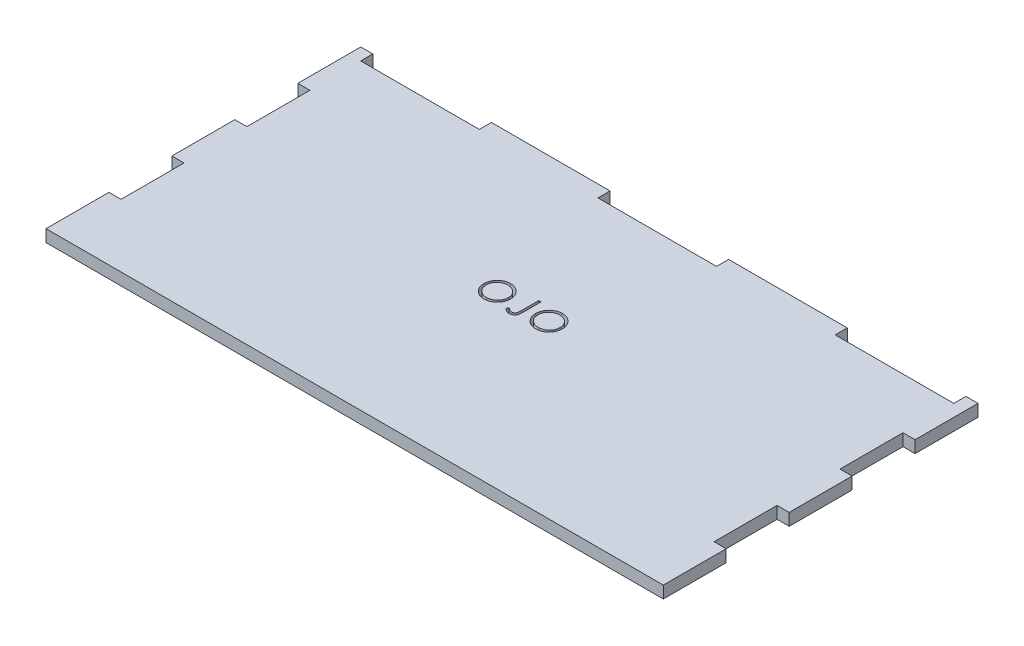
SolidWorks part; units mm, degrees
ref_plane "Front Plane" through (0, 0, 0) normal (0, 0, 1) x (1, 0, 0)
ref_plane "Top Plane" through (0, 0, 0) normal (0, 1, 0) x (1, 0, 0)
ref_plane "Right Plane" through (0, 0, 0) normal (1, 0, 0) x (0, 0, -1)
sketch "Sketch1" plane through (0, 0, 0) normal (0, 1, 0) x (1, 0, 0)
  line L6 (-73.5, 33) -> (-44.1, 33)
  line L12 (-73.5, 20.4) -> (-73.5, 4.8)
  line L14 (-76.5, 36) -> (-73.5, 36)
  line L16 (-76.5, 36) -> (-76.5, 20.4)
  line L20 (-76.5, 4.8) -> (-76.5, -10.8)
  line L23 (-76.5, -26.4) -> (-76.5, -42)
  line L24 (-76.5, -26.4) -> (-73.5, -26.4)
  line L25 (-76.5, -10.8) -> (-73.5, -10.8)
  line L26 (-76.5, 4.8) -> (-73.5, 4.8)
  line L27 (-76.5, 20.4) -> (-73.5, 20.4)
  line L29 (-73.5, 33) -> (-73.5, 36)
  line L30 (-73.5, -10.8) -> (-73.5, -26.4)
  line L31 (14.7, 36) -> (44.1, 36)
  line L32 (76.5, -26.4) -> (76.5, -42)
  line L33 (76.5, -26.4) -> (73.5, -26.4)
  line L34 (73.5, -10.8) -> (73.5, -26.4)
  line L35 (76.5, -10.8) -> (73.5, -10.8)
  line L36 (76.5, 4.8) -> (76.5, -10.8)
  line L37 (76.5, 4.8) -> (73.5, 4.8)
  line L38 (73.5, 20.4) -> (73.5, 4.8)
  line L39 (76.5, 20.4) -> (73.5, 20.4)
  line L40 (76.5, 36) -> (76.5, 20.4)
  line L41 (73.5, 33) -> (73.5, 36)
  line L43 (-14.7, 33) -> (14.7, 33)
  line L44 (73.5, 36) -> (76.5, 36)
  line L45 (44.1, 33) -> (73.5, 33)
  line L46 (-44.1, 33) -> (-44.1, 36)
  line L47 (-14.7, 33) -> (-14.7, 36)
  line L48 (14.7, 33) -> (14.7, 36)
  line L49 (44.1, 33) -> (44.1, 36)
  line L50 (-44.1, 36) -> (-14.7, 36)
  line L62 (-76.5, -42) -> (76.5, -42)
  point P0 (0, 0)
  point P4 (0, 0)
extrude "Boss-Extrude1" add sketch "Sketch1" along normal blind 3
sketch "Sketch2" plane through (0, 3, 0) normal (0, 1, 0) x (1, 0, 0)
  text T0 "OJO" font "Century Gothic" height in points 24
extrude "Cut-Extrude1" cut sketch "Sketch2" against normal through all
